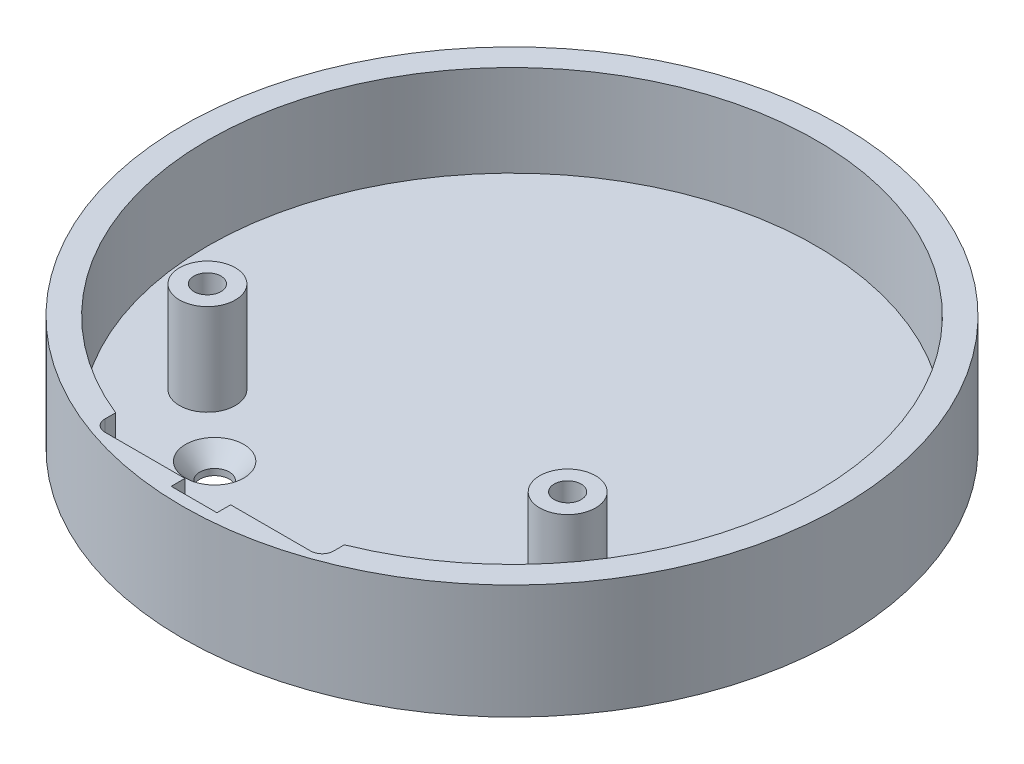
SolidWorks part; units mm, degrees
ref_plane "Front Plane" through (0, 0, 0) normal (0, 0, 1) x (1, 0, 0)
ref_plane "Top Plane" through (0, 0, 0) normal (0, 1, 0) x (1, 0, 0)
ref_plane "Right Plane" through (0, 0, 0) normal (1, 0, 0) x (0, 0, -1)
sketch "Sketch1" plane through (0, 0, 0) normal (0, 1, 0) x (1, 0, 0)
  line L0 (0, 0) -> (0, -29.6545) construction
  line L1 (-12.7, -25.527) -> (12.7, -25.527)
  line L2 (-12.7, -25.527) -> (-12.7, -33.782)
  line L3 (-12.7, -33.782) -> (12.7, -33.782)
  line L4 (12.7, -25.527) -> (12.7, -33.782)
  line L5 (12.7, -25.527) -> (-12.7, -33.782) construction
  line L6 (-20, -13.8201) -> (20, -13.8201) construction
  line L7 (-12.7, -20.32) -> (12.7, -20.32)
  circle A0 centre (0, 0) radius 35.3949
  circle A1 centre (0, 0) radius 33.7949
  circle A2 centre (-20, -13.8201) radius 1.5
  circle A3 centre (20, -13.8201) radius 1.5
  circle A4 centre (0, 0) radius 36.5949
  circle A5 centre (-20, -13.8201) radius 3.1
  circle A6 centre (20, -13.8201) radius 3.1
  point P13 (0, -13.8201)
  point P19 (0, -20.32)
  dimension "D1" = 70.7898
  dimension "D2" = 1.6
  dimension "D7" = 3
  dimension "D9" = 1.2
  dimension "D10" = 1.6
  dimension "D3" = 25.4
  dimension "D4" = 8.255
  dimension "D5" = 33.782
  dimension "D6" = 40
  dimension "D8" = 13.8201
  dimension "D11" = 25.4
  dimension "D12" = 20.32
sketch "Sketch2" plane through (0, 0, 0) normal (0, 1, 0) x (1, 0, 0)
  line L0 (12.7, -25.527) -> (12.7, -33.782) construction
  line L1 (-12.7, -25.527) -> (12.7, -25.527) construction
  line L2 (-12.7, -25.527) -> (-12.7, -33.782) construction
  line L3 (-12.7, -33.782) -> (12.7, -33.782) construction
  line L4 (12.7, -25.527) -> (12.7, -33.782)
  line L5 (-12.7, -25.527) -> (12.7, -25.527)
  line L6 (-12.7, -25.527) -> (-12.7, -33.782)
  line L7 (-12.7, -33.782) -> (12.7, -33.782)
  circle A2 centre (0, 0) radius 36.5949 construction
  circle A3 centre (0, 0) radius 36.5949
extrude "Boss-Extrude2" add sketch "Sketch2" along normal blind 2.54
sketch "Sketch3" plane through (0, 2.54, 0) normal (0, 1, 0) x (1, 0, 0)
  circle A0 centre (0, 0) radius 36.5949 construction
  circle A2 centre (0, 0) radius 36.5949
  circle A4 centre (0, 0) radius 33.7949 construction
  circle A5 centre (0, 0) radius 33.7949
extrude "Boss-Extrude3" add sketch "Sketch3" along normal blind 10.16
sketch "Sketch5" plane through (0, 2.54, 0) normal (0, 1, 0) x (1, 0, 0)
  circle A4 centre (-20, -13.8201) radius 3.1 construction
  circle A5 centre (20, -13.8201) radius 3.1 construction
  circle A6 centre (-20, -13.8201) radius 3.1
  circle A7 centre (20, -13.8201) radius 3.1
extrude "Fastener Stand Offs" add sketch "Sketch5" along normal up to surface (10.16 mm away)
sketch "Sketch6" plane through (0, 12.7, 0) normal (0, 1, 0) x (1, 0, 0)
  circle A0 centre (20, -13.8201) radius 1.5 construction
  circle A1 centre (-20, -13.8201) radius 1.5 construction
  circle A2 centre (20, -13.8201) radius 1.5
  circle A3 centre (-20, -13.8201) radius 1.5
extrude "Threaded Insert" cut sketch "Sketch6" against normal through all
hole_wizard "CSK for #4 Flat Head Machine Screw1" positions "Sketch7" profile "Sketch8" countersink size "#4" standard "ANSI Inch"
sketch "Sketch7" plane through (0, 2.54, 0) normal (0, 1, 0) x (1, 0, 0)
  point P0 (-12.7, -20.32)
  point P3 (12.7, -20.32)
sketch "Sketch8" plane through (-12.7, 2.54, 20.32) normal (1, 0, 0) x (0, 0, 1)
  line L0 (0, 0) -> (0, 2.54)
  line L1 (0, 2.54) -> (1.6319, 2.54)
  line L2 (1.6319, 2.54) -> (1.6319, 1.8481)
  line L3 (1.6319, 1.8481) -> (3.2385, 0)
  line L5 (3.2385, 0) -> (0, 0)
  line L6 (-1.6319, 1.8481) -> (-3.2385, 0) construction
  line L11 (0, -6.35) -> (0, 107.95) construction
  dimension "Thru Hole Dia." = 3.2639
  dimension "Thru Hole Depth" = 2.54
  dimension "Near C'Sink Dia." = 6.477
  dimension "Near C'Sink Angle" = 82
sketch "Sketch10" plane through (0, 2.54, 0) normal (0, -1, 0) x (1, 0, 0)
  line L0 (12.7, 33.782) -> (12.7, 25.527) construction
  line L1 (-12.7, 33.782) -> (12.7, 33.782) construction
  line L2 (12.7, 25.527) -> (-12.7, 25.527) construction
  line L3 (-12.7, 25.527) -> (-12.7, 33.782) construction
  line L4 (12.7, 33.782) -> (12.7, 25.527)
  line L5 (-12.7, 33.782) -> (-2.54, 33.782)
  line L6 (12.7, 25.527) -> (-12.7, 25.527)
  line L7 (-12.7, 25.527) -> (-12.7, 33.782)
  line L8 (2.54, 35.3036) -> (-2.54, 33.782) construction
  line L9 (-2.54, 35.3036) -> (2.54, 35.3036)
  line L10 (-2.54, 35.3036) -> (-2.54, 33.782)
  line L11 (0, 33.782) -> (2.54, 33.782) construction
  line L12 (2.54, 35.3036) -> (2.54, 33.782)
  line L13 (0, 34.5428) -> (0, 29.6545) construction
  line L14 (-2.54, 33.782) -> (0, 33.782) construction
  line L15 (2.54, 33.782) -> (12.7, 33.782)
  line L16 (-2.54, 33.782) -> (0, 33.782) construction
  line L17 (0, 33.782) -> (2.54, 33.782) construction
  circle A0 centre (0, 0) radius 35.3949 construction
  dimension "D1" = 5.08
extrude "Cut-Extrude1" cut sketch "Sketch10" against normal through all both and the other way through all
fillet "Fillet1" radius 1.27 4 edges at (12.7, 1.27, 25.527) (-12.7, 1.27, 25.527) (12.7, 6.35, 33.782) (-12.7, 6.35, 33.782)
